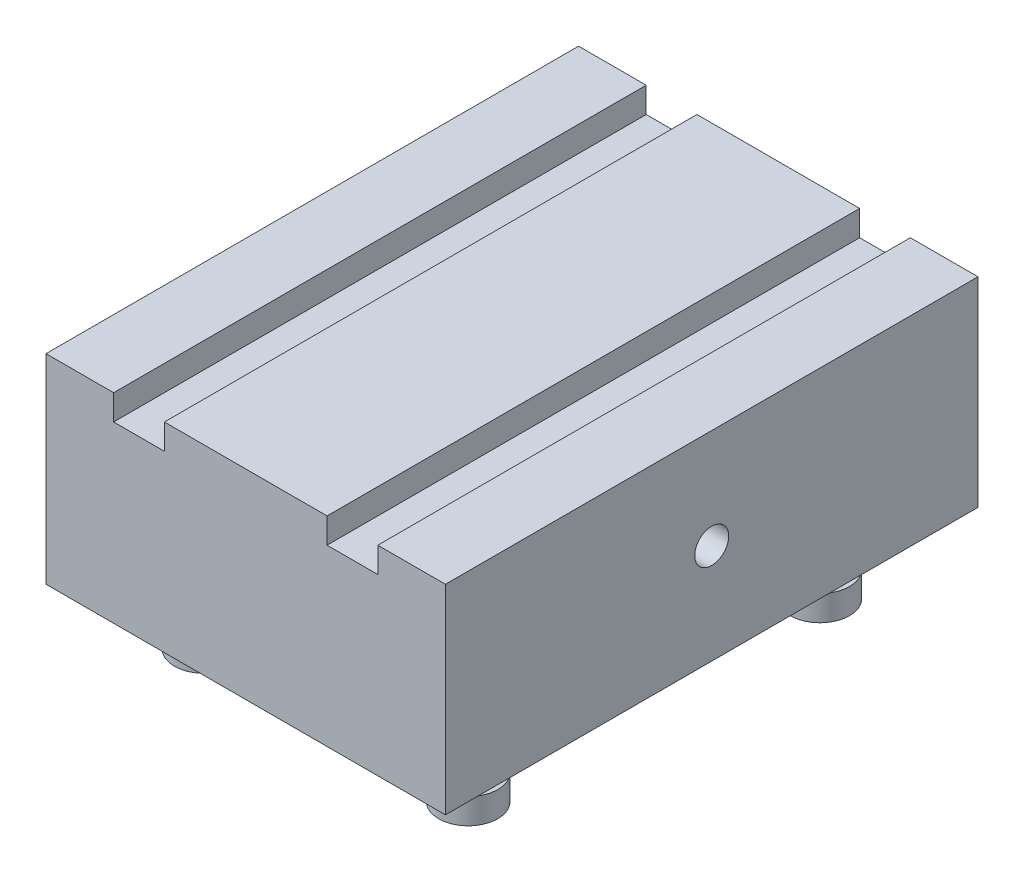
SolidWorks part; units mm, degrees
ref_plane "Front Plane" through (0, 0, 0) normal (0, 0, 1) x (1, 0, 0)
ref_plane "Top Plane" through (0, 0, 0) normal (0, 1, 0) x (1, 0, 0)
ref_plane "Right Plane" through (0, 0, 0) normal (1, 0, 0) x (0, 0, -1)
sketch "Sketch1" plane through (0, 0, 0) normal (0, 1, 0) x (1, 0, 0)
  line L1 (0, 0) -> (60, 0)
  line L2 (0, 0) -> (0, 80)
  line L3 (0, 80) -> (60, 80)
  line L4 (60, 0) -> (60, 80)
  dimension "D1" = 60
  dimension "D2" = 80
extrude "Boss-Extrude1" add sketch "Sketch1" against normal blind 30 contours L2 L3 L4 L1
sketch "Sketch2" plane through (0, 0, 0) normal (0, 0, 1) x (1, 0, 0)
  line L0 (0, 0) -> (60, 0) construction
  line L1 (10.16, 0) -> (10.16, -3.81)
  line L2 (10.16, -3.81) -> (13.97, -3.81)
  line L3 (13.97, -3.81) -> (17.78, -3.81)
  line L4 (17.78, -3.81) -> (17.78, 0)
  line L7 (30, 0) -> (30, -30) construction
  line L8 (0, -30) -> (60, -30) construction
  line L9 (42.22, -3.81) -> (42.22, 0)
  line L10 (46.03, -3.81) -> (42.22, -3.81)
  line L11 (49.84, -3.81) -> (46.03, -3.81)
  line L12 (49.84, 0) -> (49.84, -3.81)
  arc A0 (10.16, 0) -> (17.78, 0) centre (13.97, 0) ccw
  arc A1 (49.84, 0) -> (42.22, 0) centre (46.03, 0) cw
  line M4 (60, 0) -> (0, 0)
  dimension "D3" = 3.81
  dimension "D1" = 10.16
extrude "Cut-Extrude1" cut sketch "Sketch2" against normal through all contours A0 L1 L2 | A0 M4 | A0 L3 L4 | A1 M4 | L10 A1 L9 | L12 A1 L11
sketch "Sketch3" plane through (0, -30, 0) normal (0, -1, 0) x (1, 0, 0)
  line L0 (60, -40) -> (0, -40) construction
  line L1 (60, 0) -> (60, -80) construction
  line L2 (0, 0) -> (0, -80) construction
  line L3 (49.84, -18.029) -> (49.84, -61.971) construction
  line L4 (30, 0) -> (30, -80) construction
  line L5 (0, 0) -> (60, 0) construction
  line L6 (0, -80) -> (60, -80) construction
  line L7 (10.16, -18.029) -> (10.16, -61.971) construction
  circle A0 centre (49.84, -13.584) radius 4.445
  circle A1 centre (10.16, -13.584) radius 4.445
  circle A2 centre (49.84, -66.416) radius 4.445
  circle A3 centre (10.16, -66.416) radius 4.445
  point P21 (49.84, -40)
  point P24 (10.16, -40)
  dimension "D2" = 10.16
  dimension "D3" = 8.89
  dimension "D1" = 21.971
extrude "Boss-Extrude2" add sketch "Sketch3" along normal blind 3.81
sketch "Sketch4" plane through (0, -33.81, 0) normal (0, -1, 0) x (1, 0, 0)
  line L0 (60, -40) -> (0, -40) construction
  line L1 (30, 0) -> (30, -80) construction
  line L2 (0, -80) -> (60, -80) construction
  circle A0 centre (49.84, -13.584) radius 2.54
  circle A2 centre (49.84, -13.584) radius 4.445 construction
  circle A3 centre (10.16, -13.584) radius 2.54
  circle A4 centre (10.16, -66.416) radius 2.54
  circle A5 centre (49.84, -66.416) radius 2.54
  dimension "D1" = 5.08
extrude "Boss-Extrude3" add sketch "Sketch4" along normal blind 2.54
sketch "Sketch5" plane through (0, -36.35, 0) normal (0, -1, 0) x (1, 0, 0)
  line L0 (30, 0) -> (30, -80) construction
  line L1 (0, -40) -> (60, -40) construction
  circle A0 centre (10.16, -13.584) radius 4.445
  circle A1 centre (10.16, -13.584) radius 4.445 construction
  circle A2 centre (10.16, -66.416) radius 4.445
  circle A3 centre (49.84, -66.416) radius 4.445
  circle A4 centre (49.84, -13.584) radius 4.445
extrude "Boss-Extrude4" add sketch "Sketch5" along normal blind 3.81
sketch "Sketch6" plane through (60, 0, 0) normal (1, 0, 0) x (0, 0, -1)
  line L0 (40, 0) -> (40, -30) construction
  line L1 (0, 0) -> (80, 0) construction
  line L2 (0, -30) -> (80, -30) construction
  line L3 (0, -15) -> (80, -15) construction
  line L4 (0, -30) -> (0, 0) construction
  line L5 (80, -30) -> (80, 0) construction
  point P12 (40, -15)
hole_wizard "1/4-20 Tapped Hole1" positions "Sketch13" profile "Sketch14" tap size "1/4-20" standard "ANSI Inch" end condition through all
sketch "Sketch13" plane through (60, 0, 0) normal (1, 0, 0) x (0, 0, -1)
  point P0 (40, -15)
sketch "Sketch14" plane through (60, -15, -40) normal (0, 1, 0) x (0, 0, -1)
  line L0 (0, 0) -> (0, 60)
  line L1 (0, 60) -> (2.5527, 60)
  line L2 (2.5527, 60) -> (2.5527, 0)
  line L5 (2.5527, 0) -> (0, 0)
  line L11 (0, -6.35) -> (0, 107.95) construction
  dimension "Thru Tap Drill Dia." = 5.1054
  dimension "Thru Tap Drill Depth" = 60
cosmetic thread "Hole Thread3" parameters "D2"=6.35
